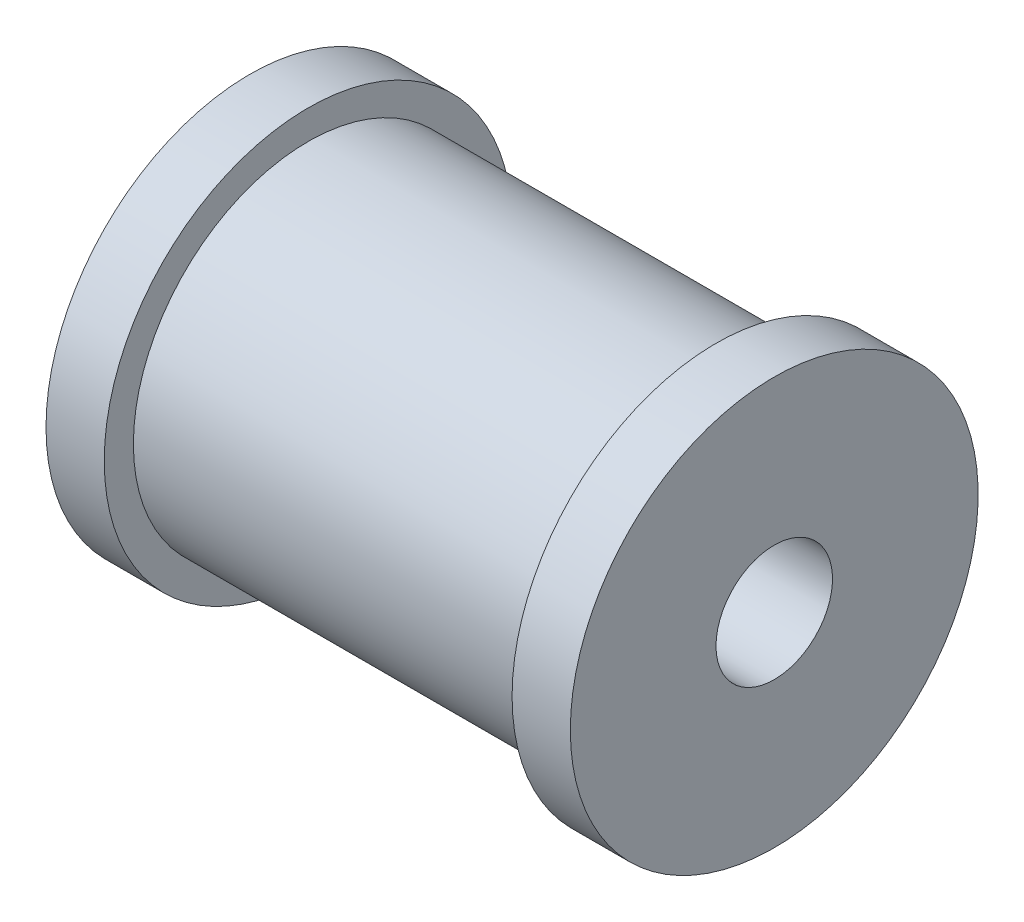
SolidWorks part; units mm, degrees
ref_plane "Front Plane" through (0, 0, 0) normal (0, 0, 1) x (1, 0, 0)
ref_plane "Top Plane" through (0, 0, 0) normal (0, 1, 0) x (1, 0, 0)
ref_plane "Right Plane" through (0, 0, 0) normal (1, 0, 0) x (0, 0, -1)
sketch "Sketch2" plane through (0, 0, 0) normal (0, 0, 1) x (1, 0, 0)
  line L0 (0, 0) -> (18, 0) construction
  line L1 (0, 2) -> (0, 7)
  line L2 (0, 7) -> (2, 7)
  line L3 (2, 7) -> (2, 6)
  line L4 (2, 6) -> (16, 6)
  line L5 (16, 6) -> (16, 7)
  line L6 (16, 7) -> (18, 7)
  line L7 (0, 2) -> (18, 2)
  line L8 (18, 2) -> (18, 7)
  dimension "D1" = 18
  dimension "D2" = 7
  dimension "D3" = 2
  dimension "D4" = 2
  dimension "D5" = 7
  dimension "D6" = 18
  dimension "D7" = 4
  dimension "D8" = 6
revolve "Revolve1" add sketch "Sketch2" angle 360 about L0
